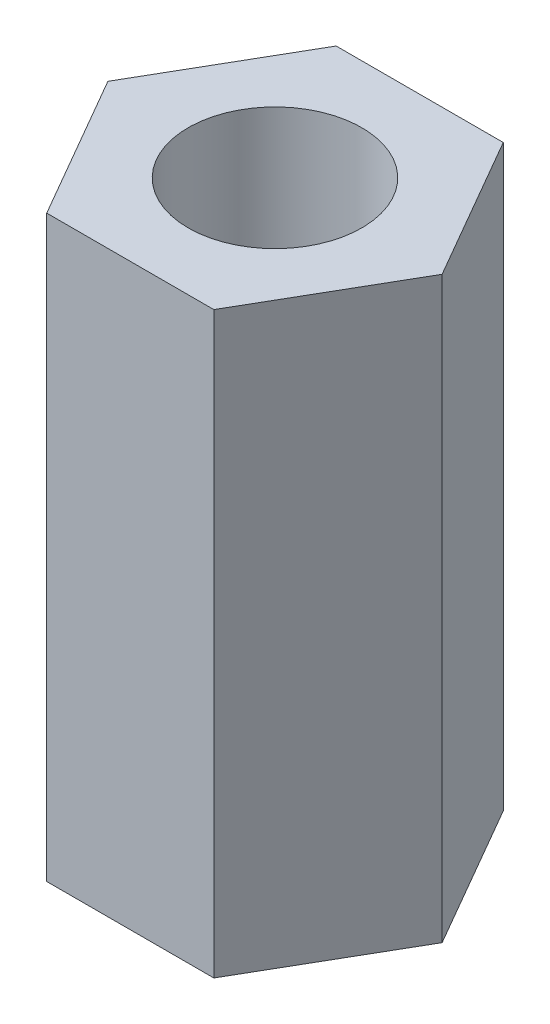
SolidWorks part; units mm, degrees
material "ABS"
ref_plane "Alzado" through (0, 0, 0) normal (0, 0, 1) x (1, 0, 0)
ref_plane "Planta" through (0, 0, 0) normal (0, 1, 0) x (1, 0, 0)
ref_plane "Vista lateral" through (0, 0, 0) normal (1, 0, 0) x (0, 0, -1)
sketch "Croquis1" plane through (0, 0, 0) normal (0, 1, 0) x (1, 0, 0)
  line L1 (1.4434, -2.5) -> (2.8868, 0)
  line L2 (2.8868, 0) -> (1.4434, 2.5)
  line L3 (1.4434, 2.5) -> (-1.4434, 2.5)
  line L4 (-1.4434, 2.5) -> (-2.8868, 0)
  line L5 (-2.8868, 0) -> (-1.4434, -2.5)
  line L6 (-1.4434, -2.5) -> (1.4434, -2.5)
  circle A0 centre (0, 0) radius 2.5 construction
  circle A1 centre (0, 0) radius 1.5
  dimension "D2" = 3
  dimension "D1" = 5
extrude "Saliente-Extruir1" add sketch "Croquis1" along normal mid plane 10
